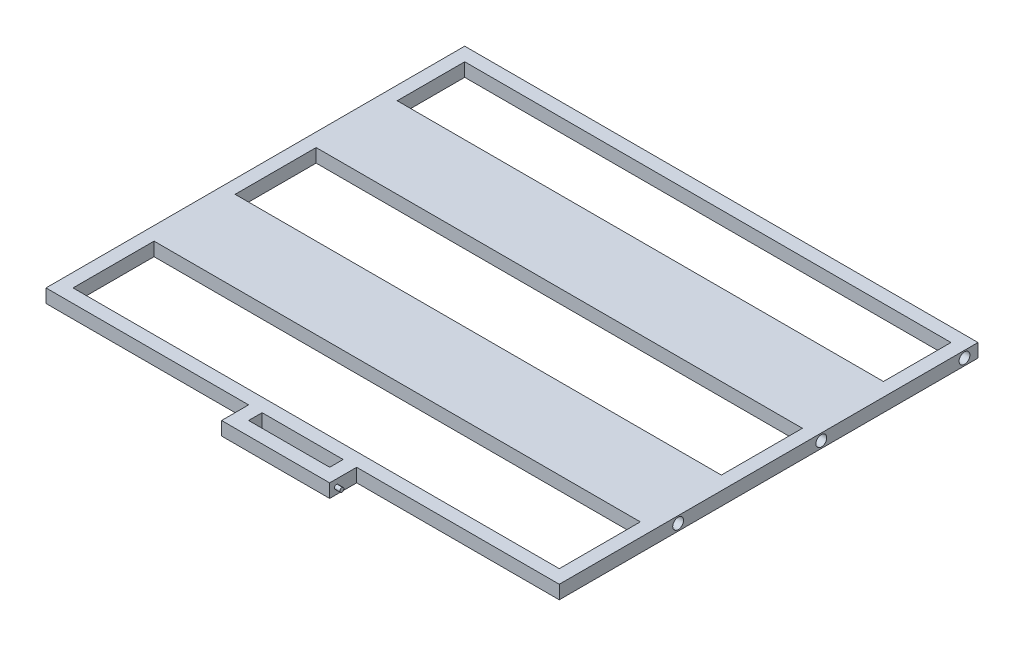
SolidWorks part; units mm, degrees
ref_plane "Alzado" through (0, 0, 0) normal (0, 0, 1) x (1, 0, 0)
ref_plane "Planta" through (0, 0, 0) normal (0, 1, 0) x (1, 0, 0)
ref_plane "Vista lateral" through (0, 0, 0) normal (1, 0, 0) x (0, 0, -1)
sketch "Croquis1" plane through (0, 0, 0) normal (0, 1, 0) x (1, 0, 0)
  line L0 (-450, 225) -> (450, 225)
  line L1 (-475, -400) -> (475, -400)
  line L2 (-475, -400) -> (-475, 400)
  line L3 (-475, 400) -> (475, 400)
  line L4 (475, -400) -> (475, 400)
  line L5 (-475, -400) -> (475, 400) construction
  line L6 (-475, 400) -> (475, -400) construction
  line L7 (-450, -375) -> (450, -375)
  line L8 (-450, -375) -> (-450, 375)
  line L9 (-450, 375) -> (450, 375)
  line L10 (450, -375) -> (450, 375)
  line L11 (-450, -375) -> (450, 375) construction
  line L12 (-450, 375) -> (450, -375) construction
  line L13 (-450, 75) -> (450, 75)
  line L14 (-450, -75) -> (450, -75)
  line L15 (-450, -225) -> (450, -225)
  line L16 (-450, 375) -> (-450, 225) construction
  line L17 (0, -400) -> (100, -400) construction
  line L18 (0, -400) -> (-100, -400) construction
  line L19 (-100, -400) -> (-100, -450)
  line L20 (-100, -450) -> (100, -450)
  line L21 (100, -450) -> (100, -400)
  line L22 (-100, -425) -> (100, -425)
  line L23 (-75, -400) -> (-75, -450)
  line L24 (75, -400) -> (75, -450)
  point P0 (0, 0)
  point P6 (0, 0)
  dimension "D1" = 950
  dimension "D2" = 800
  dimension "D3" = 900
  dimension "D4" = 750
  dimension "D6" = 150
  dimension "D7" = 100
  dimension "D8" = 200
  dimension "D9" = 50
  dimension "D10" = 25
  dimension "D11" = 25
  dimension "D5" = 5
extrude "Saliente-Extruir1" add sketch "Croquis1" along normal blind 25 contours L1 L4 L3 L2 L10 L7 L8 L9 | L8 L13 L10 L0 | L8 L15 L10 L14 | L24 L22 L23 L20 | L23 L22 L19 L20 | L23 L1 L19 L22 | L1 L24 L22 L21 | L22 L24 L20 L21
sketch "Croquis2" plane through (100, 0, 0) normal (1, 0, 0) x (0, 0, -1)
  line L0 (-450, 0) -> (-450, 25)
  line L1 (-450, 25) -> (-425, 25)
  line L2 (-450, 25) -> (-400, 25) construction
  line L3 (-425, 25) -> (-425, 0)
  line L4 (-450, 0) -> (-400, 0) construction
  line L5 (-425, 0) -> (-450, 25)
  circle A0 centre (-437.5, 12.5) radius 3.75
  dimension "D2" = 7.5
  dimension "D1" = 25
extrude "Saliente-Extruir2" add sketch "Croquis2" along normal blind 10 contours L5 A0 | L5 A0
sketch "Croquis3" plane through (-450, 0, 0) normal (1, 0, 0) x (0, 0, -1)
  line L0 (375, 0) -> (350, 0) construction
  line L1 (225, 0) -> (375, 0) construction
  line L2 (350, 0) -> (350, 25)
  line L3 (225, 25) -> (375, 25) construction
  line L4 (350, 25) -> (375, 25)
  line L5 (375, 25) -> (375, 0)
  line L6 (375, 0) -> (350, 0)
  dimension "D1" = 25
extrude "Saliente-Extruir3" add sketch "Croquis3" along normal through all
sketch "Croquis4" plane through (-475, 0, 0) normal (-1, 0, 0) x (0, 0, 1)
  line L0 (-375, 25) -> (-375, 0)
  line L1 (400, 25) -> (-400, 25) construction
  line L2 (400, 0) -> (-400, 0) construction
  line L3 (-400, 25) -> (-400, 0) construction
  line L4 (-375, 0) -> (-400, 0)
  line L5 (-400, 0) -> (-400, 25)
  line L6 (-400, 25) -> (-375, 25)
  dimension "D1" = 25
extrude "Cortar-Extruir1" cut sketch "Croquis4" against normal through all
sketch "Croquis5" plane through (475, 0, 0) normal (1, 0, 0) x (0, 0, -1)
  line L0 (325, 25) -> (325, 0) construction
  line L1 (-400, 25) -> (375, 25) construction
  line L2 (-400, 0) -> (375, 0) construction
  line L3 (375, 0) -> (375, 25) construction
  line L4 (325, 0) -> (375, 25) construction
  line L5 (350, 12.5) -> (85, 12.5) construction
  circle A0 centre (350, 12.5) radius 10
  circle A1 centre (85, 12.5) radius 10
  circle A2 centre (-180, 12.5) radius 10
  dimension "D2" = 20
  dimension "D1" = 50
  dimension "D4" = 265
  dimension "D3" = 3
extrude "Cortar-Extruir2" cut sketch "Croquis5" against normal blind 20
ref_plane "Plano1" through (-1.2097, -319.2133, 1311.8917) normal (1, 0, 0) x (0, -0.2871, -0.9579)
mirror "Simetría1" about plane through (-1.2097, -319.2133, 1311.8917) normal (1, 0, 0) of "Cortar-Extruir2"
